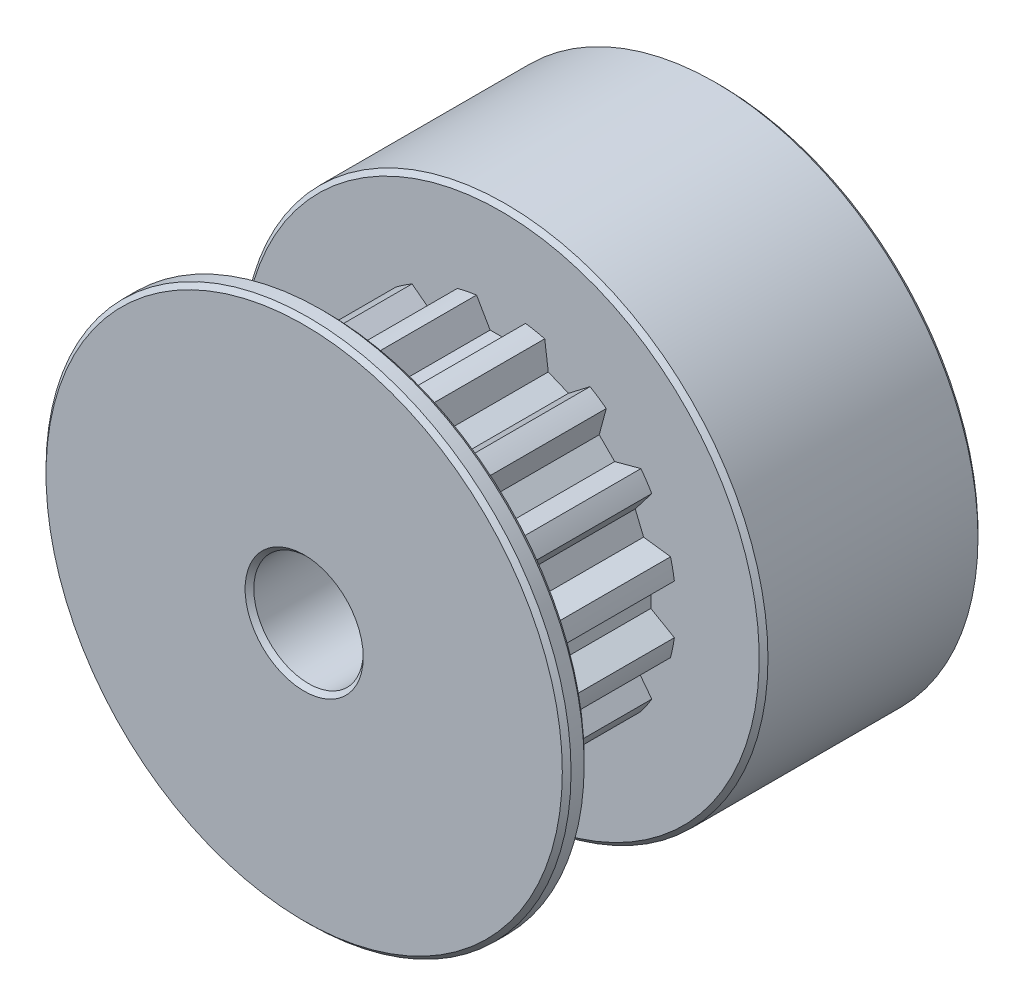
SolidWorks part; units mm, degrees
ref_plane "Plan de face" through (0, 0, 0) normal (0, 0, 1) x (1, 0, 0)
ref_plane "Plan de dessus" through (0, 0, 0) normal (0, 1, 0) x (1, 0, 0)
ref_plane "Plan de droite" through (0, 0, 0) normal (1, 0, 0) x (0, 0, -1)
sketch "Esquisse1" plane through (0, 0, 0) normal (0, 0, 1) x (1, 0, 0)
  circle A0 centre (0, 0) radius 8
  dimension "D1" = 16
extrude "Boss.-Extru.1" add sketch "Esquisse1" along normal blind 8
sketch "Esquisse2" plane through (0, 0, 8) normal (0, 0, 1) x (1, 0, 0)
  line L0 (0, 10.6124) -> (0, -10.8862) construction
  line L1 (-1.1208, 7.9211) -> (-0.5, 6.8459)
  line L2 (-0.5, 6.8459) -> (0.5, 6.8459)
  line L3 (0.5, 6.8459) -> (1.1208, 7.9211)
  circle A0 centre (0, 0) radius 8 construction
  arc A1 (-1.1208, 7.9211) -> (1.1208, 7.9211) centre (0, 0) cw
  dimension "D1" = 1
  dimension "D2" = 0.5
  dimension "D3" = 60
  dimension "D4" = 120
extrude "Enlèv. mat.-Extru.1" cut sketch "Esquisse2" against normal through all
pattern_circular "Répétition circulaire1" count 16 over 360 about axis through (0, 0, 0) along (0, 0, 1) of "Enlèv. mat.-Extru.1"
sketch "Esquisse3" plane through (0, 0, 0) normal (0, 0, -1) x (-1, 0, 0)
  circle A0 centre (0, 0) radius 12
  dimension "D1" = 24
extrude "Boss.-Extru.2" add sketch "Esquisse3" along normal blind 10
sketch "Esquisse4" plane through (0, 0, 8) normal (0, 0, 1) x (1, 0, 0)
  circle A0 centre (0, 0) radius 12
  dimension "D1" = 24
extrude "Boss.-Extru.3" add sketch "Esquisse4" along normal blind 1
chamfer "Chanfrein1" distance 0.2 angle 45 4 edges at (-12, 0, -10) (-12, 0, 0) (12, 0, 8) (12, 0, 9)
sketch "Esquisse5" plane through (0, 0, -10) normal (0, 0, -1) x (-1, 0, 0)
  circle A0 centre (0, 0) radius 2.5
  dimension "D1" = 5
extrude "Enlèv. mat.-Extru.2" cut sketch "Esquisse5" against normal through all
chamfer "Chanfrein2" distance 0.2 angle 45 2 edges at (-2.5, 0, -10) (-2.5, 0, 9)
